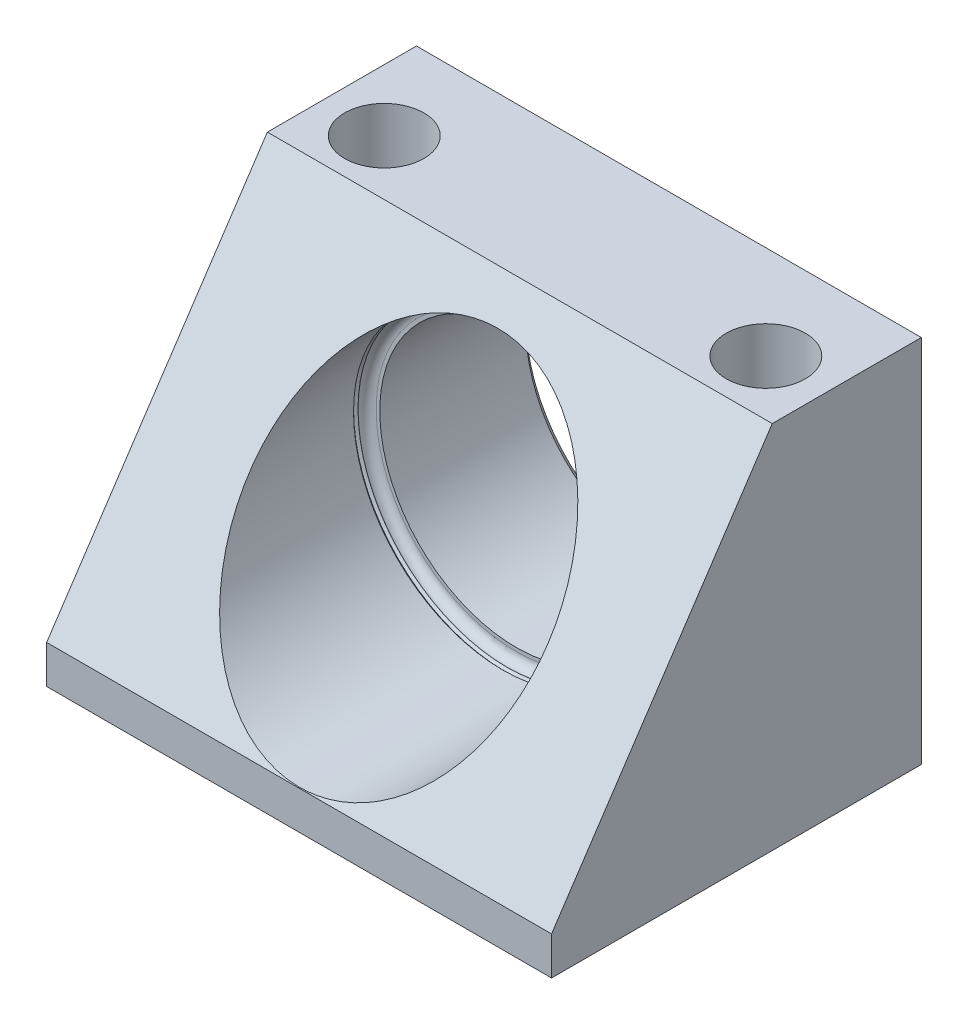
SolidWorks part; units mm, degrees
material "Alloy Steel"
ref_plane "Front Plane" through (0, 0, 0) normal (0, 0, 1) x (1, 0, 0)
ref_plane "Top Plane" through (0, 0, 0) normal (0, 1, 0) x (1, 0, 0)
ref_plane "Right Plane" through (0, 0, 0) normal (1, 0, 0) x (0, 0, -1)
sketch "Sketch1" plane through (0, 0, 0) normal (0, 0, 1) x (1, 0, 0)
  line L0 (0, 0) -> (0, 30.988) construction
  line L1 (-43.0022, 30.988) -> (43.0022, 30.988)
  line L2 (-43.0022, 30.988) -> (-43.0022, -32.004)
  line L3 (-43.0022, -32.004) -> (43.0022, -32.004)
  line L4 (43.0022, 30.988) -> (43.0022, -32.004)
  circle A0 centre (0, 0) radius 23.2665
  dimension "D4" = 46.533
  dimension "D1" = 86.0044
  dimension "D2" = 62.992
  dimension "D3" = 32.004
extrude "Extrude1" add sketch "Sketch1" against normal blind 62.992
sketch "Sketch2" plane through (43.0022, 0, 0) normal (1, 0, 0) x (0, 0, -1)
  line L0 (0, 30.988) -> (37.592, 30.988)
  line L3 (62.992, 30.988) -> (0, 30.988) construction
  line L4 (37.592, 30.988) -> (0, -25.5016)
  line L5 (0, -32.004) -> (0, 30.988) construction
  line L6 (0, -25.5016) -> (0, 30.988)
  line L7 (62.992, -32.004) -> (62.992, 30.988) construction
  line L8 (62.992, -32.004) -> (0, -32.004) construction
  dimension "D2" = 6.5024
  dimension "D1" = 25.4
extrude "Cut-Extrude1" cut sketch "Sketch2" against normal through all
sketch "Sketch3" plane through (0, 0, 0) normal (0, 0, -1) x (-1, 0, 0)
  circle A0 centre (0, 0) radius 25.4
  dimension "D1" = 50.8
extrude "Cut-Extrude2" cut sketch "Sketch3" along normal offset from surface (37.0078 mm away) 25.9842 up to face at (23.2665, 0, -62.992)
fillet "Fillet1" radius 1.524 1 edges at (25.4, 0, -37.0078)
hole_wizard "Hole1" positions "Sketch5" profile "Sketch4" legacy end condition up to next
sketch "Sketch5" plane through (0, 30.988, 0) normal (0, 1, 0) x (-1, 0, 0)
  line L0 (-43.0022, -62.992) -> (-43.0022, -37.592) construction
  line L2 (-43.0022, -62.992) -> (43.0022, -62.992) construction
  point P0 (32.512, -47.0154)
  point P1 (-32.4866, -47.0154)
  dimension "D1" = 10.5156
  dimension "D2" = 15.9766
  dimension "D3" = 64.9986
sketch "Sketch4" plane through (-32.512, 30.988, -47.0154) normal (1, 0, 0) x (0, 0, 1)
  line L0 (0, 0) -> (0, 62.992)
  line L1 (0, 62.992) -> (6.7437, 62.992)
  line L2 (6.7437, 62.992) -> (6.7437, 0)
  line L3 (6.7437, 0) -> (0, 0)
  line L4 (0, 110) -> (0, -10) construction
  dimension "Diameter" = 13.4874
  dimension "Depth" = 62.992
ref_plane "Plane1" through (0, 0, 0) normal (0, 1, 0) x (-1, 0, 0)
sketch "Sketch6" plane through (0, 0, 0) normal (0, 1, 0) x (-1, 0, 0)
  line L0 (25.4, -34.671) -> (25.4, -35.433)
  line L1 (25.4, -35.4838) -> (25.4, -16.9705) construction
  line L2 (25.4, -35.433) -> (25.781, -35.052)
  line L3 (25.781, -35.052) -> (25.4, -34.671)
  line L4 (0, 17.5081) -> (0, -67.5449) construction
  line L5 (0, -62.992) -> (0, -37.0078) construction
  line L6 (-43.0022, -62.992) -> (43.0022, -62.992) construction
  line L7 (23.2665, -61.8745) -> (23.2665, -62.992)
  line L9 (23.2665, -62.992) -> (24.384, -62.992)
  line L10 (24.384, -62.992) -> (23.2665, -61.8745)
  line L12 (23.2665, -62.992) -> (23.2665, -37.0078) construction
  dimension "D1" = 90
  dimension "D2" = 45
  dimension "D3" = 0.762
  dimension "D4" = 27.94
  dimension "D5" = 45
  dimension "D6" = 48.768
revolve "Cut-Revolve1" cut sketch "Sketch6" angle 360 about L4
